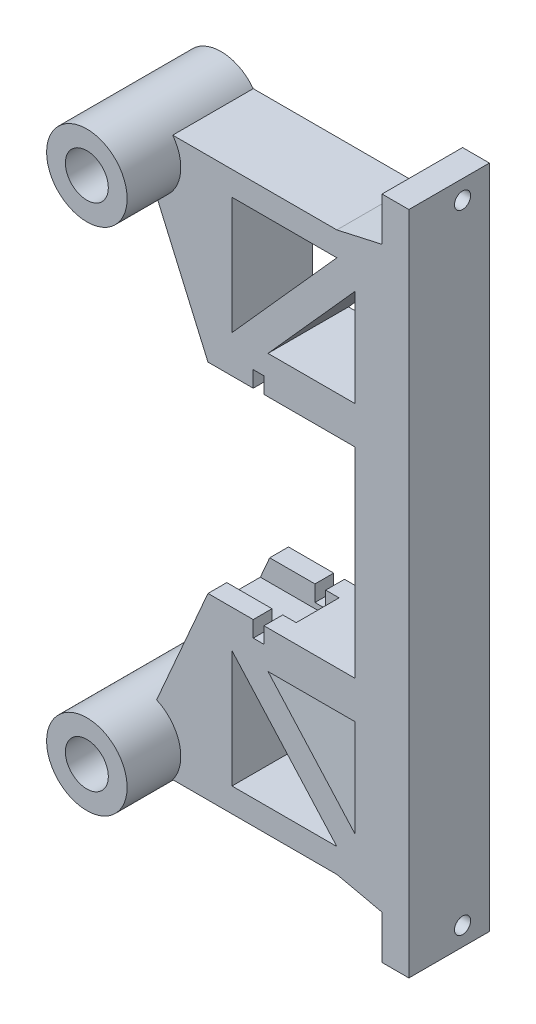
SolidWorks part; units mm, degrees
ref_plane "Alzado" through (0, 0, 0) normal (0, 0, 1) x (1, 0, 0)
ref_plane "Planta" through (0, 0, 0) normal (0, 1, 0) x (1, 0, 0)
ref_plane "Vista lateral" through (0, 0, 0) normal (1, 0, 0) x (0, 0, -1)
sketch "Croquis1" plane through (0, 0, 0) normal (0, 0, 1) x (1, 0, 0)
  line L0 (8.6705, 85.1618) -> (-5.9329, 85.1618) construction
  line L4 (8.6705, 47.8382) -> (-5.9329, 47.8382) construction
  line L12 (28.5, 85.1618) -> (28.5, 47.8382)
  line L15 (38.5, 121.5) -> (38.5, 11.5)
  line L17 (38.5, 121.5) -> (38.5, 128.5)
  line L25 (28.5, 22.6765) -> (28.5, 40.8382)
  line L26 (28.5, 110.3235) -> (28.5, 92.1618)
  line L27 (28.5, 110.3235) -> (12.25, 92.1618)
  line L28 (12.25, 40.8382) -> (28.5, 22.6765)
  line L29 (28.5, 92.1618) -> (12.25, 92.1618)
  line L30 (25.0802, 114) -> (5.5408, 92.1618)
  line L31 (28.5, 40.8382) -> (12.25, 40.8382)
  line L34 (5.5408, 40.8382) -> (25.0802, 19)
  line L43 (5.5408, 114) -> (25.0802, 114)
  line L44 (5.5408, 19) -> (25.0802, 19)
  line L47 (33.5, 123.4103) -> (1.0671, 87.1618) construction
  line L48 (33.5, 123.4103) -> (33.5, 87.1618) construction
  line L49 (33.5, 87.1618) -> (1.0671, 87.1618) construction
  line L52 (1.0671, 45.8382) -> (33.5, 9.5897) construction
  line L53 (33.5, 9.5897) -> (33.5, 45.8382) construction
  line L54 (33.5, 45.8382) -> (1.0671, 45.8382) construction
  line L55 (28.5, 85.1618) -> (11.5, 85.1618)
  line L61 (-5.5, 118.5) -> (25.0802, 118.5)
  line L62 (33.5, 12.6178) -> (25.0802, 14.5)
  line L63 (28.5, 47.8382) -> (11.5, 47.8382)
  line L67 (-5.5, 14.5) -> (25.0802, 14.5)
  line L68 (33.5, 120.3822) -> (25.0802, 118.5)
  line L69 (1.0671, 85.1618) -> (-8.5038, 107.1245)
  line L70 (1.0671, 47.8382) -> (-8.5038, 25.8755)
  line L71 (-5.9329, 121) -> (40.7363, 121) construction
  line L72 (40.7363, 121) -> (8.6705, 85.1618) construction
  line L73 (-5.9329, 85.1618) -> (-5.9329, 121) construction
  line L74 (8.6705, 47.8382) -> (40.7363, 12) construction
  line L75 (-5.9329, 12) -> (40.7363, 12) construction
  line L76 (-5.9329, 47.8382) -> (-5.9329, 12) construction
  line L77 (5.5408, 92.1618) -> (5.5408, 114)
  line L78 (5.5408, 40.8382) -> (5.5408, 19)
  line L79 (1.0671, 114) -> (25.0802, 114) construction
  line L80 (1.0671, 19) -> (25.0802, 19) construction
  line L81 (38.5, 128.5) -> (33.5, 128.5)
  line L82 (33.5, 128.5) -> (33.5, 120.3822)
  line L83 (38.5, 11.5) -> (38.5, 4.5)
  line L84 (38.5, 4.5) -> (33.5, 4.5)
  line L85 (33.5, 4.5) -> (33.5, 12.6178)
  line L86 (1.0671, 92.1618) -> (1.0671, 114) construction
  line L87 (5.5408, 92.1618) -> (1.0671, 92.1618) construction
  line L88 (5.5408, 40.8382) -> (1.0671, 40.8382) construction
  line L89 (1.0671, 40.8382) -> (1.0671, 19) construction
  line L90 (11.5, 88.1618) -> (9.5, 88.1618)
  line L91 (9.5, 44.8382) -> (11.5, 44.8382)
  line L92 (9.5, 85.1618) -> (1.0671, 85.1618)
  line L93 (11.5, 47.8382) -> (11.5, 44.8382)
  line L94 (11.5, 85.1618) -> (11.5, 88.1618)
  line L95 (9.5, 47.8382) -> (9.5, 44.8382)
  line L96 (9.5, 85.1618) -> (9.5, 88.1618)
  line L97 (9.5, 47.8382) -> (1.0671, 47.8382)
  circle A2 centre (-11.5, 114) radius 4
  circle A3 centre (-11.5, 19) radius 4
  arc A4 (-5.5, 118.5) -> (-8.5038, 107.1245) centre (-11.5, 114) ccw
  arc A5 (-8.5038, 25.8755) -> (-5.5, 14.5) centre (-11.5, 19) ccw
  dimension "D2" = 15
  dimension "D4" = 8
  dimension "D3" = 15
  dimension "D5" = 95
  dimension "D6" = 5
  dimension "D7" = 7
  dimension "D8" = 7
  dimension "D10" = 5
  dimension "D12" = 5
  dimension "D13" = 3
  dimension "D14" = 3
  dimension "D9" = 7
  dimension "D11" = 7
extrude "Saliente-Extruir2" add sketch "Croquis1" along normal blind 15
sketch "Croquis2" plane through (0, 0, 15) normal (0, 0, 1) x (1, 0, 0)
  circle A0 centre (-11.5, 114) radius 7.5
  circle A1 centre (-11.5, 19) radius 7.5
  circle A2 centre (-11.5, 114) radius 4
  circle A3 centre (-11.5, 19) radius 4
extrude "Saliente-Extruir3" add sketch "Croquis2" along normal blind 10
sketch "Croquis3" plane through (0, 0, 0) normal (0, 0, -1) x (-1, 0, 0)
  circle A0 centre (11.5, 114) radius 4.0065
  circle A1 centre (11.5, 19) radius 4.004
extrude "Saliente-Extruir4" add sketch "Croquis3" against normal blind 2
sketch "Croquis4" plane through (33.5, 0, 0) normal (-1, 0, 0) x (0, 0, 1)
  circle A0 centre (5, 125) radius 1.5
  circle A1 centre (5, 8) radius 1.5
  dimension "D1" = 3
  dimension "D2" = 3
extrude "Cortar-Extruir1" cut sketch "Croquis4" against normal through all
sketch "Croquis5" plane through (11.5, 0, 0) normal (-1, 0, 0) x (0, 0, 1)
  line L0 (3.5, 85.1618) -> (11.5, 85.1618)
  line L1 (3.5, 47.8382) -> (11.5, 47.8382)
  line L7 (11.5, 85.1618) -> (11.5, 89.1618)
  line L8 (11.5, 89.1618) -> (3.5, 89.1618)
  line L9 (3.5, 89.1618) -> (3.5, 85.1618)
  line L10 (3.5, 47.8382) -> (3.5, 43.8382)
  line L11 (3.5, 43.8382) -> (11.5, 43.8382)
  line L12 (11.5, 43.8382) -> (11.5, 47.8382)
  dimension "D1" = 4
  dimension "D2" = 4
extrude "Cortar-Extruir2" cut sketch "Croquis5" along normal blind 15 and the other way blind 2.5
